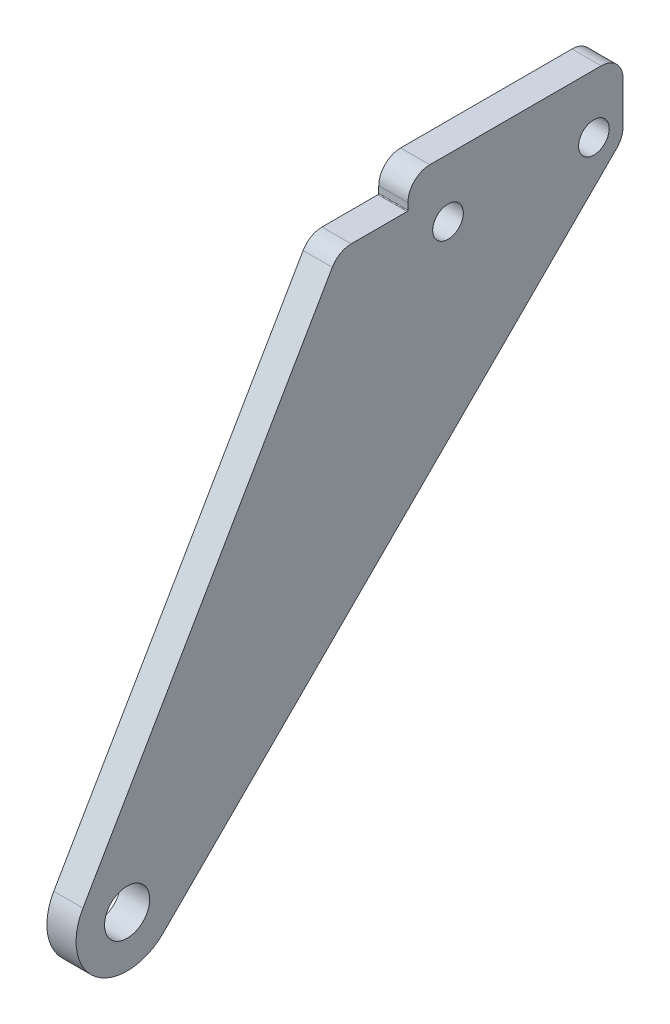
SolidWorks part; units mm, degrees
material "Hexcel AS4C (3000 丝)"
ref_plane "前视基准面" through (0, 0, 0) normal (0, 0, 1) x (1, 0, 0)
ref_plane "上视基准面" through (0, 0, 0) normal (0, 1, 0) x (1, 0, 0)
ref_plane "右视基准面" through (0, 0, 0) normal (1, 0, 0) x (0, 0, -1)
sketch "草图1" plane through (0, 0, 0) normal (1, 0, 0) x (0, 0, -1)
  line L0 (44, 60) -> (64, 60) construction
  line L1 (-6.0564, 3.5099) -> (29, 64)
  line L2 (29, 64) -> (74, 64)
  line L3 (74, 64) -> (4.9461, -4.9534)
  circle A0 centre (0, 0) radius 3.1
  circle A1 centre (44, 60) radius 2.1
  circle A2 centre (64, 60) radius 2.1
  arc A3 (-6.0564, 3.5099) -> (4.9461, -4.9534) centre (0, 0) ccw
  dimension "D1" = 6.2
  dimension "D2" = 4.2
  dimension "D7" = 14
  dimension "D3" = 44
  dimension "D4" = 60
  dimension "D6" = 20
  dimension "D8" = 4
  dimension "D9" = 15
  dimension "D10" = 45
  dimension "D5" = 2
extrude "凸台-拉伸1" add sketch "草图1" along normal blind 4
sketch "草图2" plane through (4, 0, 0) normal (1, 0, 0) x (0, 0, -1)
  line L1 (74, 64) -> (38.5, 64)
  line L2 (74, 64) -> (74, 68)
  line L3 (74, 68) -> (38.5, 68)
  line L4 (38.5, 64) -> (38.5, 68)
  line L5 (56.25, 68) -> (56.25, 64) construction
  line L6 (74, 66) -> (38.5, 66) construction
  point P96 (56.25, 66)
  dimension "D1" = 4
  dimension "D2" = 35.5
extrude "凸台-拉伸2" add sketch "草图2" against normal up to surface (4 mm away) up to face at (0, 30.4325, -24.5442)
sketch "草图3" plane through (4, 0, 0) normal (1, 0, 0) x (0, 0, -1)
  line L0 (74, 68) -> (68, 68)
  line L1 (74, 68) -> (38.5, 68) construction
  line L2 (68, 68) -> (68, 58.0087)
  line L3 (4.9461, -4.9534) -> (74, 64) construction
  line L4 (68, 58.0087) -> (74, 64)
  line L5 (74, 64) -> (74, 68)
  dimension "D1" = 6
extrude "切除-拉伸1" cut sketch "草图3" against normal through all
fillet "圆角1" radius 3 4 edges at (2, 68, -38.5) (2, 64, -29) (2, 58.0087, -68) (2, 68, -68)
fillet "圆角2" radius 0.1 1 edges at (2, 64, -38.5)
